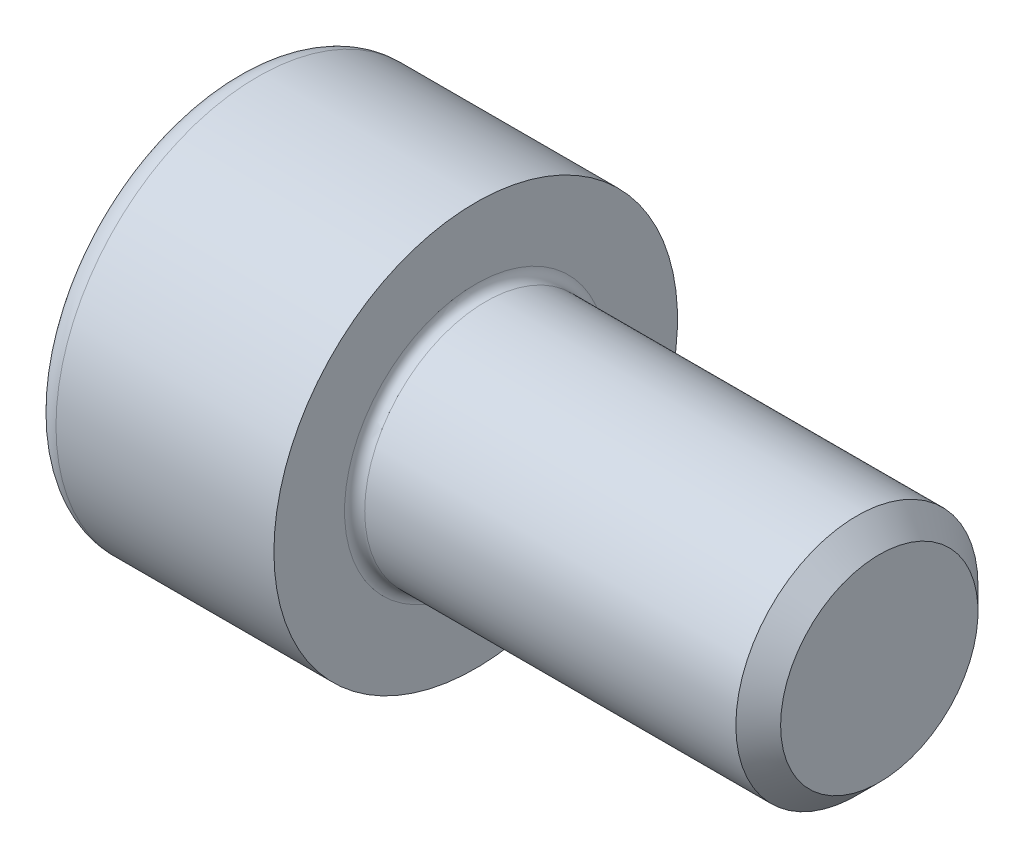
SolidWorks part; units mm, degrees
ref_plane "Plane1" through (0, 0, 0) normal (0, 0, 1) x (1, 0, 0)
ref_plane "Plane2" through (0, 0, 0) normal (0, 1, 0) x (1, 0, 0)
ref_plane "Plane3" through (0, 0, 0) normal (1, 0, 0) x (0, 0, -1)
sketch "BodySke" plane through (0, 0, 0) normal (0, 0, 1) x (1, 0, 0)
  line L0 (0, 0) -> (0, 5)
  line L1 (0, 5) -> (6, 5)
  line L2 (6, 5) -> (6, 3)
  line L3 (6, 3) -> (15.4455, 3)
  line L4 (16, 2.4455) -> (16, 0)
  line L5 (16, 0) -> (0, 0)
  line L6 (-31.75, 0) -> (127, 0) construction
  line L8 (16, 2.4455) -> (15.4455, 3)
  line L10 (16, -2.4455) -> (15.4455, -3) construction
  line L11 (7, 9.525) -> (7, 3.175) construction
  line L12 (6, 9.525) -> (6, 3.175) construction
  line L13 (-44, 9.525) -> (-44, 3.175) construction
  dimension "Diameter" = 6
  dimension "Head_ht" = 6
  dimension "Length" = 10
  dimension "Body_ch_ang" = 45
  dimension "Head_dia" = 10
  dimension "Minor_dia" = 4.891
  dimension "Advance" = 1
  dimension "Thread_nom" = 10
  dimension "Thread_length" = 60
revolve "Base-Revolve" add sketch "BodySke"
cosmetic thread "ThreadCosmetic" [suppressed]
fillet "Fillet1" radius 0.25 1 edges at (6, 0, 3)
fillet "Fillet2" radius 0.6 1 edges at (0, 0, 5)
sketch "Sketch2" plane through (0, 0, 0) normal (0, 0, 1) x (1, 0, 0)
  line L0 (0, 2.51) -> (3, 2.51)
  line L1 (3, 2.51) -> (4.4491, 0)
  line L2 (-31.75, 0) -> (127, 0) construction
  line L3 (4.4491, 0) -> (0, 0)
  line L4 (0, 0) -> (0, 2.51)
  line L6 (0, 0) -> (47.625, 0) construction
  dimension "D1" = 2.51
  dimension "D2" = 60
  dimension "Depth" = 3
revolve "Hex-PreBroach" cut sketch "Sketch2" angle 360 about L6
sketch "Sketch3" plane through (0, 0, 0) normal (-1, 0, 0) x (0, 0.5, 0.866)
  line L0 (1.4491, 2.51) -> (-1.4491, 2.51)
  line L1 (-1.4491, 2.51) -> (-2.8983, 0)
  line L2 (1.4491, 2.51) -> (2.8983, 0)
  line L3 (1.4491, -2.51) -> (2.8983, 0)
  line L4 (1.4491, -2.51) -> (-1.4491, -2.51)
  line L5 (-1.4491, -2.51) -> (-2.8983, 0)
  dimension "D1" = 2.51
  dimension "D2" = 2.51
  dimension "Hex_size" = 5.02
extrude "Hex" cut sketch "Sketch3" against normal blind 3
sketch "ThdSchSke" plane through (0, 0, 0) normal (0, 0, 1) x (1, 0, 0)
  line L0 (9, -2.4455) -> (8.6117, -3)
  line L1 (9, -2.4455) -> (9.3883, -3)
  line L2 (9.3883, -3) -> (9.3883, -3.75)
  line L3 (-3.175, 0) -> (5.1513, 0) construction
  line L4 (0, 4.4) -> (0, -4.4) construction
  line L5 (9.3883, -3.75) -> (8.6117, -3.75)
  line L6 (8.6117, -3.75) -> (8.6117, -3)
  dimension "Thread_minor" = 4.891
  dimension "Diameter" = 6
  dimension "Start" = 9
  dimension "SideAngle" = 55
  dimension "VeeAngle" = 70
  dimension "Overcut" = 7.5
revolve "ThreadSchematic" [suppressed] cut sketch "ThdSchSke" angle 360 about L3
pattern_linear "ThdSchPat" [suppressed]
equation "\"D2@Sketch3\" = \"Hex_size@Sketch3\" / 2"
equation "\"D1@Sketch3\" = \"Hex_size@Sketch3\" / 2"
equation "\"D1@Sketch2\" = \"Hex_size@Sketch3\" / 2"
equation "\"Thread_minor@ThreadCosmetic\"  =  \"Minor_dia@BodySke\""
equation "\"Depth@Sketch2\" =  \"Key_eng@Hex\""
equation "\"Thread_length@ThreadCosmetic\" = ((sgn( (\"Length@BodySke\" - \"Advance@BodySke\" * 3.0) - \"Thread_nom@BodySke\" )-1)*( (\"Length@BodySke\" - \"Advance@BodySke\" * 3.0) - \"Thread_nom@BodySke\" ))/-2+ \"Thread_nom@BodySke\""
equation "\"Thread_minor@ThdSchSke\" = \"Minor_dia@BodySke\""
equation "\"Diameter@ThdSchSke\" = \"Diameter@BodySke\""
equation "\"Overcut@ThdSchSke\" = \"Diameter@BodySke\" * 1.25"
equation "\"Start@ThdSchSke\" = \"Head_ht@BodySke\" + \"Length@BodySke\" - \"Thread_length@ThreadCosmetic\"  '---Non-countersunk---"
equation "\"Num_threads@ThdSchPat\" = int( \"Thread_length@ThreadCosmetic\" / \"Advance@BodySke\" + 0.999 )  + 1"
equation "\"Advance@ThdSchPat\" = \"Thread_length@ThreadCosmetic\" /  (\"Num_threads@ThdSchPat\" - 1) 'relax it"
equation "\"Num_threads@ThdSchPat\" = \"Num_threads@ThdSchPat\" - sgn( \"Num_threads@ThdSchPat\" - 1) '---chamfered tips only---"
